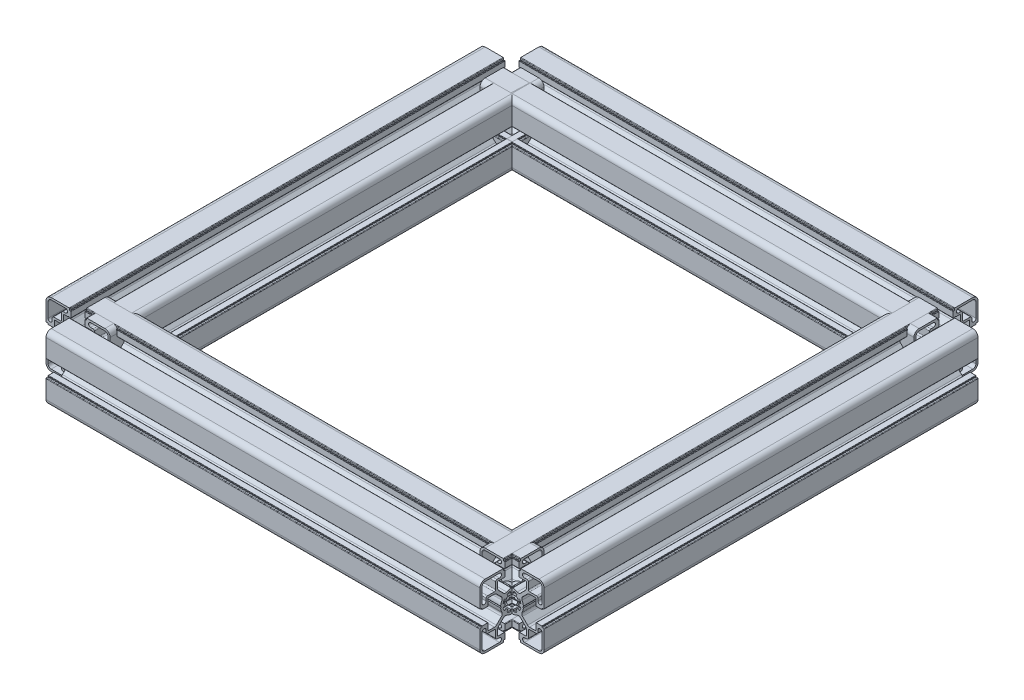
SolidWorks part; units mm, degrees
ref_plane "Front Plane" through (0, 0, 0) normal (0, 0, 1) x (1, 0, 0)
ref_plane "Top Plane" through (0, 0, 0) normal (0, 1, 0) x (1, 0, 0)
ref_plane "Right Plane" through (0, 0, 0) normal (1, 0, 0) x (0, 0, -1)
sketch "Sketch1" plane through (0, 0, 0) normal (0, 1, 0) x (1, 0, 0)
  line L0 (0, 0) -> (-304.8, 0)
  line L1 (-304.8, 0) -> (-304.8, 304.8)
  line L2 (-304.8, 304.8) -> (0, 304.8)
  line L3 (0, 304.8) -> (0, 0)
  dimension "D1" = 304.8
  dimension "D2" = 304.8
other "Aluminum extrusions 45MM SQUARE EXTRUSION 10MM T SLOT LIGHT(1)"
ref_plane "Plane1" through (-304.8, 0, 0) normal (0, 0, -1) x (-1, 0, 0)
sketch "Sketch11" plane through (-304.8, 0, 0) normal (0, 0, -1) x (-1, 0, 0)
  line L0 (12.4425, 11.5) -> (17.2075, 11.5)
  line L1 (11.5, 17.2075) -> (11.5, 12.4425)
  line L2 (8.7938, 18.15) -> (10.5575, 18.15)
  line L3 (18.875, 21.05) -> (8.7938, 21.05)
  line L4 (-1.1678, -5.8711) -> (-0.9755, -4.9039)
  line L5 (-2.7779, -4.1573) -> (-3.3257, -4.9773)
  line L6 (-4.9773, -3.3257) -> (-4.1573, -2.7779)
  line L7 (-4.9039, -0.9755) -> (-5.8711, -1.1678)
  line L8 (-5.8711, 1.1678) -> (-4.9039, 0.9755)
  line L9 (-4.1573, 2.7779) -> (-4.9773, 3.3257)
  line L10 (-3.3257, 4.9773) -> (-2.7779, 4.1573)
  line L11 (-0.9755, 4.9039) -> (-1.1678, 5.8711)
  line L12 (1.1678, 5.8711) -> (0.9755, 4.9039)
  line L13 (2.7779, 4.1573) -> (3.3257, 4.9773)
  line L14 (4.9773, 3.3257) -> (4.1573, 2.7779)
  line L15 (4.9039, 0.9755) -> (5.8711, 1.1678)
  line L16 (5.8711, -1.1678) -> (4.9039, -0.9755)
  line L17 (4.1573, -2.7779) -> (4.9773, -3.3257)
  line L18 (3.3257, -4.9773) -> (2.7779, -4.1573)
  line L19 (0.9755, -4.9039) -> (1.1678, -5.8711)
  line L20 (21.05, 8.7938) -> (21.05, 18.875)
  line L21 (18.15, 10.5575) -> (18.15, 8.7938)
  line L22 (-12.4425, -11.5) -> (-17.2075, -11.5)
  line L23 (-11.5, -17.2075) -> (-11.5, -12.4425)
  line L24 (-8.7938, -18.15) -> (-10.5575, -18.15)
  line L25 (-18.875, -21.05) -> (-8.7938, -21.05)
  line L26 (-21.05, -8.7938) -> (-21.05, -18.875)
  line L27 (-18.15, -10.5575) -> (-18.15, -8.7938)
  line L28 (6.1619, 16.7) -> (6.5969, 17.135)
  line L29 (6.5969, 17.135) -> (7.0319, 16.7)
  line L30 (7.0319, 16.7) -> (9.673, 16.7)
  line L31 (10.05, 16.323) -> (10.05, 12.2808)
  line L32 (9.4979, 10.9479) -> (5.9549, 7.4049)
  line L33 (0.5529, 7.9809) -> (0, 7.5937)
  line L34 (0, 7.5937) -> (-0.5529, 7.9809)
  line L35 (-5.9549, 7.4049) -> (-9.4979, 10.9479)
  line L36 (-10.05, 12.2808) -> (-10.05, 16.323)
  line L37 (-9.673, 16.7) -> (-5.377, 16.7)
  line L38 (-5, 17.077) -> (-5, 20.8615)
  line L39 (-5.1885, 21.05) -> (-5.6615, 21.05)
  line L40 (-5.85, 21.2385) -> (-5.85, 22.123)
  line L41 (-6.227, 22.5) -> (-18.875, 22.5)
  line L42 (-22.5, 18.875) -> (-22.5, 6.227)
  line L43 (-22.123, 5.85) -> (-21.2385, 5.85)
  line L44 (-21.05, 5.6615) -> (-21.05, 5.1885)
  line L45 (-20.8615, 5) -> (-17.077, 5)
  line L46 (-16.7, 5.377) -> (-16.7, 9.673)
  line L47 (-16.323, 10.05) -> (-12.2808, 10.05)
  line L48 (-10.9479, 9.4979) -> (-7.4049, 5.9549)
  line L49 (-7.9809, 0.5529) -> (-7.5937, 0)
  line L50 (-7.5937, 0) -> (-7.9809, -0.5529)
  line L51 (-7.4049, -5.9549) -> (-10.9479, -9.4979)
  line L52 (-12.2808, -10.05) -> (-16.323, -10.05)
  line L53 (-16.7, -9.673) -> (-16.7, -5.377)
  line L54 (-17.077, -5) -> (-20.8615, -5)
  line L55 (-21.05, -5.1885) -> (-21.05, -5.6615)
  line L56 (-21.2385, -5.85) -> (-22.123, -5.85)
  line L57 (-22.5, -6.227) -> (-22.5, -18.875)
  line L58 (-18.875, -22.5) -> (-6.227, -22.5)
  line L59 (-5.85, -22.123) -> (-5.85, -21.2385)
  line L60 (-5.6615, -21.05) -> (-5.1885, -21.05)
  line L61 (-5, -20.8615) -> (-5, -17.077)
  line L62 (-5.377, -16.7) -> (-9.673, -16.7)
  line L63 (-10.05, -16.323) -> (-10.05, -12.2808)
  line L64 (-9.4979, -10.9479) -> (-5.9549, -7.4049)
  line L65 (-0.5529, -7.9809) -> (0, -7.5937)
  line L66 (0, -7.5937) -> (0.5529, -7.9809)
  line L67 (5.9549, -7.4049) -> (9.4979, -10.9479)
  line L68 (10.05, -12.2808) -> (10.05, -16.323)
  line L69 (9.673, -16.7) -> (5.377, -16.7)
  line L70 (5, -17.077) -> (5, -20.8615)
  line L71 (5.1885, -21.05) -> (5.6615, -21.05)
  line L72 (5.85, -21.2385) -> (5.85, -22.123)
  line L73 (6.227, -22.5) -> (18.875, -22.5)
  line L74 (22.5, -18.875) -> (22.5, -6.227)
  line L75 (22.123, -5.85) -> (21.2385, -5.85)
  line L76 (21.05, -5.6615) -> (21.05, -5.1885)
  line L77 (20.8615, -5) -> (17.077, -5)
  line L78 (16.7, -5.377) -> (16.7, -9.673)
  line L79 (16.323, -10.05) -> (12.2808, -10.05)
  line L80 (10.9479, -9.4979) -> (7.4049, -5.9549)
  line L81 (7.9809, -0.5529) -> (7.5937, 0)
  line L82 (7.5937, 0) -> (7.9809, 0.5529)
  line L83 (7.4049, 5.9549) -> (10.9479, 9.4979)
  line L84 (12.2808, 10.05) -> (16.323, 10.05)
  line L85 (16.7, 9.673) -> (16.7, 5.377)
  line L86 (17.077, 5) -> (20.8615, 5)
  line L87 (21.05, 5.1885) -> (21.05, 5.6615)
  line L88 (21.2385, 5.85) -> (22.123, 5.85)
  line L89 (22.5, 6.227) -> (22.5, 18.875)
  line L90 (18.875, 22.5) -> (6.227, 22.5)
  line L91 (5.85, 22.123) -> (5.85, 21.2385)
  line L92 (5.6615, 21.05) -> (5.1885, 21.05)
  line L93 (5, 20.8615) -> (5, 17.077)
  line L94 (5.377, 16.7) -> (6.1619, 16.7)
  line L95 (-18.15, 8.7938) -> (-18.15, 10.5575)
  line L96 (-21.05, 18.875) -> (-21.05, 8.7938)
  line L97 (-8.7938, 21.05) -> (-18.875, 21.05)
  line L98 (-10.5575, 18.15) -> (-8.7938, 18.15)
  line L99 (-11.5, 12.4425) -> (-11.5, 17.2075)
  line L100 (-17.2075, 11.5) -> (-12.4425, 11.5)
  line L101 (18.15, -8.7938) -> (18.15, -10.5575)
  line L102 (21.05, -18.875) -> (21.05, -8.7938)
  line L103 (8.7938, -21.05) -> (18.875, -21.05)
  line L104 (10.5575, -18.15) -> (8.7938, -18.15)
  line L105 (11.5, -12.4425) -> (11.5, -17.2075)
  line L106 (17.2075, -11.5) -> (12.4425, -11.5)
  line L107 (-6.227, 22.5) -> (6.227, 22.5) construction
  line L108 (22.5, 6.227) -> (22.5, -6.227) construction
  line L109 (6.227, -22.5) -> (-6.227, -22.5) construction
  line L110 (-22.5, -6.227) -> (-22.5, 6.227) construction
  arc A0 (18.15, 10.5575) -> (17.2075, 11.5) centre (17.2075, 10.5575) ccw
  arc A1 (11.5, 12.4425) -> (12.4425, 11.5) centre (12.4425, 12.4425) ccw
  arc A2 (11.5, 17.2075) -> (10.5575, 18.15) centre (10.5575, 17.2075) ccw
  arc A3 (8.7938, 21.05) -> (8.7938, 18.15) centre (8.7938, 19.6) ccw
  arc A4 (21.05, 18.875) -> (18.875, 21.05) centre (18.875, 18.875) ccw
  arc A5 (18.15, 8.7938) -> (21.05, 8.7938) centre (19.6, 8.7938) ccw
  arc A6 (-18.15, -10.5575) -> (-17.2075, -11.5) centre (-17.2075, -10.5575) ccw
  arc A7 (-11.5, -12.4425) -> (-12.4425, -11.5) centre (-12.4425, -12.4425) ccw
  arc A8 (-11.5, -17.2075) -> (-10.5575, -18.15) centre (-10.5575, -17.2075) ccw
  arc A9 (-8.7938, -21.05) -> (-8.7938, -18.15) centre (-8.7938, -19.6) ccw
  arc A10 (-21.05, -18.875) -> (-18.875, -21.05) centre (-18.875, -18.875) ccw
  arc A11 (-18.15, -8.7938) -> (-21.05, -8.7938) centre (-19.6, -8.7938) ccw
  arc A12 (-1.6342, -6.162) -> (-1.1678, -5.8711) centre (-1.5376, -5.7976) ccw
  arc A13 (-3.2016, -5.5128) -> (-1.6342, -6.162) centre (0, 0) ccw
  arc A14 (-3.3257, -4.9773) -> (-3.2016, -5.5128) centre (-3.0123, -5.1867) ccw
  arc A15 (-4.1573, -2.7779) -> (-2.7779, -4.1573) centre (0, 0) ccw
  arc A16 (10.05, 16.323) -> (9.673, 16.7) centre (9.673, 16.323) ccw
  arc A17 (9.4979, 10.9479) -> (10.05, 12.2808) centre (8.165, 12.2808) ccw
  arc A18 (3.7407, 7.0716) -> (5.9549, 7.4049) centre (4.622, 8.7378) ccw
  arc A19 (3.7407, 7.0716) -> (0.5529, 7.9809) centre (0, 0) ccw
  arc A20 (-0.5529, 7.9809) -> (-3.7407, 7.0716) centre (0, 0) ccw
  arc A21 (-5.9549, 7.4049) -> (-3.7407, 7.0716) centre (-4.622, 8.7378) ccw
  arc A22 (-10.05, 12.2808) -> (-9.4979, 10.9479) centre (-8.165, 12.2808) ccw
  arc A23 (-9.673, 16.7) -> (-10.05, 16.323) centre (-9.673, 16.323) ccw
  arc A24 (-5.377, 16.7) -> (-5, 17.077) centre (-5.377, 17.077) ccw
  arc A25 (-5, 20.8615) -> (-5.1885, 21.05) centre (-5.1885, 20.8615) ccw
  arc A26 (-5.85, 21.2385) -> (-5.6615, 21.05) centre (-5.6615, 21.2385) ccw
  arc A27 (-5.85, 22.123) -> (-6.227, 22.5) centre (-6.227, 22.123) ccw
  arc A28 (-18.875, 22.5) -> (-22.5, 18.875) centre (-18.875, 18.875) ccw
  arc A29 (-22.5, 6.227) -> (-22.123, 5.85) centre (-22.123, 6.227) ccw
  arc A30 (-21.05, 5.6615) -> (-21.2385, 5.85) centre (-21.2385, 5.6615) ccw
  arc A31 (-21.05, 5.1885) -> (-20.8615, 5) centre (-20.8615, 5.1885) ccw
  arc A32 (-17.077, 5) -> (-16.7, 5.377) centre (-17.077, 5.377) ccw
  arc A33 (-16.323, 10.05) -> (-16.7, 9.673) centre (-16.323, 9.673) ccw
  arc A34 (-10.9479, 9.4979) -> (-12.2808, 10.05) centre (-12.2808, 8.165) ccw
  arc A35 (-7.0716, 3.7407) -> (-7.4049, 5.9549) centre (-8.7378, 4.622) ccw
  arc A36 (-7.0716, 3.7407) -> (-7.9809, 0.5529) centre (0, 0) ccw
  arc A37 (-7.9809, -0.5529) -> (-7.0716, -3.7407) centre (0, 0) ccw
  arc A38 (-7.4049, -5.9549) -> (-7.0716, -3.7407) centre (-8.7378, -4.622) ccw
  arc A39 (-12.2808, -10.05) -> (-10.9479, -9.4979) centre (-12.2808, -8.165) ccw
  arc A40 (-16.7, -9.673) -> (-16.323, -10.05) centre (-16.323, -9.673) ccw
  arc A41 (-16.7, -5.377) -> (-17.077, -5) centre (-17.077, -5.377) ccw
  arc A42 (-20.8615, -5) -> (-21.05, -5.1885) centre (-20.8615, -5.1885) ccw
  arc A43 (-21.2385, -5.85) -> (-21.05, -5.6615) centre (-21.2385, -5.6615) ccw
  arc A44 (-22.123, -5.85) -> (-22.5, -6.227) centre (-22.123, -6.227) ccw
  arc A45 (-22.5, -18.875) -> (-18.875, -22.5) centre (-18.875, -18.875) ccw
  arc A46 (-6.227, -22.5) -> (-5.85, -22.123) centre (-6.227, -22.123) ccw
  arc A47 (-5.6615, -21.05) -> (-5.85, -21.2385) centre (-5.6615, -21.2385) ccw
  arc A48 (-5.1885, -21.05) -> (-5, -20.8615) centre (-5.1885, -20.8615) ccw
  arc A49 (-5, -17.077) -> (-5.377, -16.7) centre (-5.377, -17.077) ccw
  arc A50 (-10.05, -16.323) -> (-9.673, -16.7) centre (-9.673, -16.323) ccw
  arc A51 (-9.4979, -10.9479) -> (-10.05, -12.2808) centre (-8.165, -12.2808) ccw
  arc A52 (-3.7407, -7.0716) -> (-5.9549, -7.4049) centre (-4.622, -8.7378) ccw
  arc A53 (-3.7407, -7.0716) -> (-0.5529, -7.9809) centre (0, 0) ccw
  arc A54 (0.5529, -7.9809) -> (3.7407, -7.0716) centre (0, 0) ccw
  arc A55 (5.9549, -7.4049) -> (3.7407, -7.0716) centre (4.622, -8.7378) ccw
  arc A56 (10.05, -12.2808) -> (9.4979, -10.9479) centre (8.165, -12.2808) ccw
  arc A57 (9.673, -16.7) -> (10.05, -16.323) centre (9.673, -16.323) ccw
  arc A58 (5.377, -16.7) -> (5, -17.077) centre (5.377, -17.077) ccw
  arc A59 (5, -20.8615) -> (5.1885, -21.05) centre (5.1885, -20.8615) ccw
  arc A60 (5.85, -21.2385) -> (5.6615, -21.05) centre (5.6615, -21.2385) ccw
  arc A61 (5.85, -22.123) -> (6.227, -22.5) centre (6.227, -22.123) ccw
  arc A62 (18.875, -22.5) -> (22.5, -18.875) centre (18.875, -18.875) ccw
  arc A63 (22.5, -6.227) -> (22.123, -5.85) centre (22.123, -6.227) ccw
  arc A64 (21.05, -5.6615) -> (21.2385, -5.85) centre (21.2385, -5.6615) ccw
  arc A65 (21.05, -5.1885) -> (20.8615, -5) centre (20.8615, -5.1885) ccw
  arc A66 (17.077, -5) -> (16.7, -5.377) centre (17.077, -5.377) ccw
  arc A67 (16.323, -10.05) -> (16.7, -9.673) centre (16.323, -9.673) ccw
  arc A68 (10.9479, -9.4979) -> (12.2808, -10.05) centre (12.2808, -8.165) ccw
  arc A69 (7.0716, -3.7407) -> (7.4049, -5.9549) centre (8.7378, -4.622) ccw
  arc A70 (7.0716, -3.7407) -> (7.9809, -0.5529) centre (0, 0) ccw
  arc A71 (7.9809, 0.5529) -> (7.0716, 3.7407) centre (0, 0) ccw
  arc A72 (7.4049, 5.9549) -> (7.0716, 3.7407) centre (8.7378, 4.622) ccw
  arc A73 (12.2808, 10.05) -> (10.9479, 9.4979) centre (12.2808, 8.165) ccw
  arc A74 (16.7, 9.673) -> (16.323, 10.05) centre (16.323, 9.673) ccw
  arc A75 (16.7, 5.377) -> (17.077, 5) centre (17.077, 5.377) ccw
  arc A76 (20.8615, 5) -> (21.05, 5.1885) centre (20.8615, 5.1885) ccw
  arc A77 (21.2385, 5.85) -> (21.05, 5.6615) centre (21.2385, 5.6615) ccw
  arc A78 (22.123, 5.85) -> (22.5, 6.227) centre (22.123, 6.227) ccw
  arc A79 (22.5, 18.875) -> (18.875, 22.5) centre (18.875, 18.875) ccw
  arc A80 (6.227, 22.5) -> (5.85, 22.123) centre (6.227, 22.123) ccw
  arc A81 (5.6615, 21.05) -> (5.85, 21.2385) centre (5.6615, 21.2385) ccw
  arc A82 (5.1885, 21.05) -> (5, 20.8615) centre (5.1885, 20.8615) ccw
  arc A83 (5, 17.077) -> (5.377, 16.7) centre (5.377, 17.077) ccw
  arc A84 (-5.5128, -3.2016) -> (-4.9773, -3.3257) centre (-5.1867, -3.0123) ccw
  arc A85 (-6.162, -1.6342) -> (-5.5128, -3.2016) centre (0, 0) ccw
  arc A86 (-5.8711, -1.1678) -> (-6.162, -1.6342) centre (-5.7976, -1.5376) ccw
  arc A87 (-4.9039, 0.9755) -> (-4.9039, -0.9755) centre (0, 0) ccw
  arc A88 (-6.162, 1.6342) -> (-5.8711, 1.1678) centre (-5.7976, 1.5376) ccw
  arc A89 (-5.5128, 3.2016) -> (-6.162, 1.6342) centre (0, 0) ccw
  arc A90 (-4.9773, 3.3257) -> (-5.5128, 3.2016) centre (-5.1867, 3.0123) ccw
  arc A91 (-2.7779, 4.1573) -> (-4.1573, 2.7779) centre (0, 0) ccw
  arc A92 (-3.2016, 5.5128) -> (-3.3257, 4.9773) centre (-3.0123, 5.1867) ccw
  arc A93 (-1.6342, 6.162) -> (-3.2016, 5.5128) centre (0, 0) ccw
  arc A94 (-1.1678, 5.8711) -> (-1.6342, 6.162) centre (-1.5376, 5.7976) ccw
  arc A95 (0.9755, 4.9039) -> (-0.9755, 4.9039) centre (0, 0) ccw
  arc A96 (1.6342, 6.162) -> (1.1678, 5.8711) centre (1.5376, 5.7976) ccw
  arc A97 (3.2016, 5.5128) -> (1.6342, 6.162) centre (0, 0) ccw
  arc A98 (3.3257, 4.9773) -> (3.2016, 5.5128) centre (3.0123, 5.1867) ccw
  arc A99 (4.1573, 2.7779) -> (2.7779, 4.1573) centre (0, 0) ccw
  arc A100 (5.5128, 3.2016) -> (4.9773, 3.3257) centre (5.1867, 3.0123) ccw
  arc A101 (6.162, 1.6342) -> (5.5128, 3.2016) centre (0, 0) ccw
  arc A102 (5.8711, 1.1678) -> (6.162, 1.6342) centre (5.7976, 1.5376) ccw
  arc A103 (4.9039, -0.9755) -> (4.9039, 0.9755) centre (0, 0) ccw
  arc A104 (6.162, -1.6342) -> (5.8711, -1.1678) centre (5.7976, -1.5376) ccw
  arc A105 (5.5128, -3.2016) -> (6.162, -1.6342) centre (0, 0) ccw
  arc A106 (4.9773, -3.3257) -> (5.5128, -3.2016) centre (5.1867, -3.0123) ccw
  arc A107 (2.7779, -4.1573) -> (4.1573, -2.7779) centre (0, 0) ccw
  arc A108 (3.2016, -5.5128) -> (3.3257, -4.9773) centre (3.0123, -5.1867) ccw
  arc A109 (1.6342, -6.162) -> (3.2016, -5.5128) centre (0, 0) ccw
  arc A110 (1.1678, -5.8711) -> (1.6342, -6.162) centre (1.5376, -5.7976) ccw
  arc A111 (-0.9755, -4.9039) -> (0.9755, -4.9039) centre (0, 0) ccw
  arc A112 (-17.2075, 11.5) -> (-18.15, 10.5575) centre (-17.2075, 10.5575) ccw
  arc A113 (-21.05, 8.7938) -> (-18.15, 8.7938) centre (-19.6, 8.7938) ccw
  arc A114 (-18.875, 21.05) -> (-21.05, 18.875) centre (-18.875, 18.875) ccw
  arc A115 (-8.7938, 18.15) -> (-8.7938, 21.05) centre (-8.7938, 19.6) ccw
  arc A116 (-10.5575, 18.15) -> (-11.5, 17.2075) centre (-10.5575, 17.2075) ccw
  arc A117 (-12.4425, 11.5) -> (-11.5, 12.4425) centre (-12.4425, 12.4425) ccw
  arc A118 (17.2075, -11.5) -> (18.15, -10.5575) centre (17.2075, -10.5575) ccw
  arc A119 (21.05, -8.7938) -> (18.15, -8.7938) centre (19.6, -8.7938) ccw
  arc A120 (18.875, -21.05) -> (21.05, -18.875) centre (18.875, -18.875) ccw
  arc A121 (8.7938, -18.15) -> (8.7938, -21.05) centre (8.7938, -19.6) ccw
  arc A122 (10.5575, -18.15) -> (11.5, -17.2075) centre (10.5575, -17.2075) ccw
  arc A123 (12.4425, -11.5) -> (11.5, -12.4425) centre (12.4425, -12.4425) ccw
  point P355 (0, 0)
